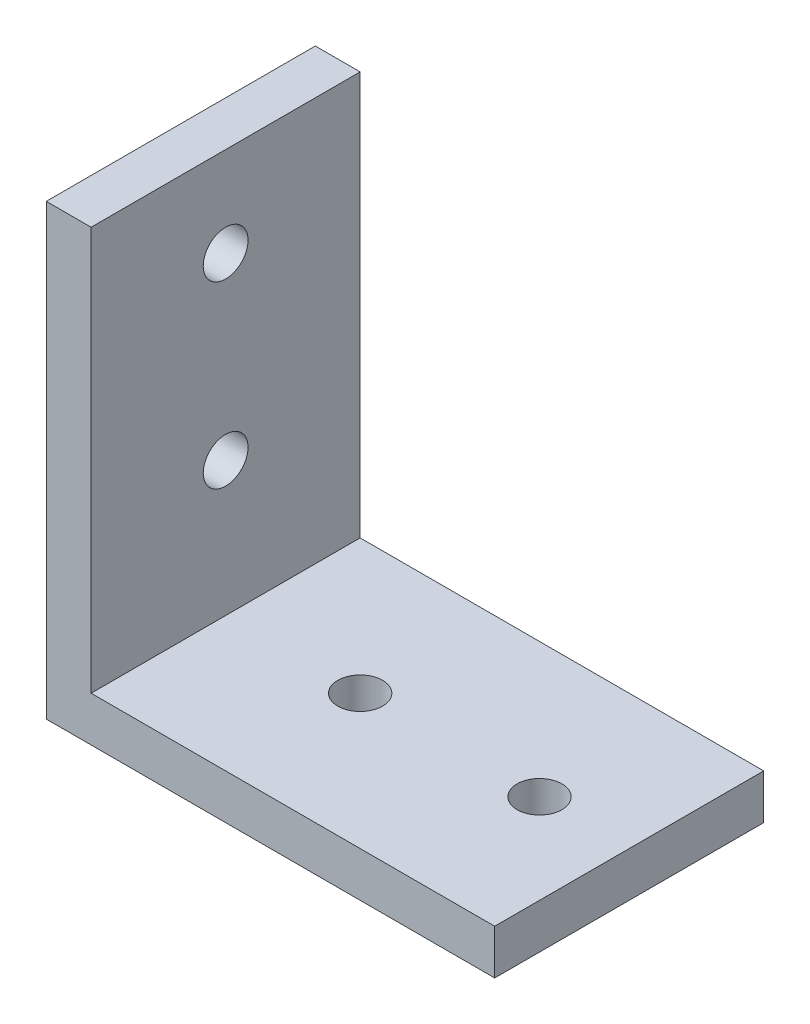
SolidWorks part; units mm, degrees
material "Plain Carbon Steel"
ref_plane "Front Plane" through (0, 0, 0) normal (0, 0, 1) x (1, 0, 0)
ref_plane "Top Plane" through (0, 0, 0) normal (0, 1, 0) x (1, 0, 0)
ref_plane "Right Plane" through (0, 0, 0) normal (1, 0, 0) x (0, 0, -1)
sketch "Sketch1" plane through (0, 0, 0) normal (0, 0, 1) x (1, 0, 0)
  line L0 (0, 0) -> (0, 100)
  line L1 (0, 100) -> (10, 100)
  line L2 (10, 100) -> (10, 10)
  line L3 (10, 10) -> (100, 10)
  line L4 (100, 10) -> (100, 0)
  line L5 (100, 0) -> (0, 0)
  dimension "D1" = 10
  dimension "D2" = 100
  dimension "D3" = 100
extrude "Boss-Extrude1" add sketch "Sketch1" along normal mid plane 60
sketch "Sketch2" plane through (10, 0, 0) normal (1, 0, 0) x (0, 0, -1)
  line L0 (-30, 0) -> (30, 0) construction
  line L1 (0, 55) -> (0, -55) construction
  circle A0 centre (0, 40) radius 5
  circle A1 centre (0, 80) radius 5
  dimension "D1" = 10
  dimension "D2" = 40
  dimension "D3" = 80
extrude "Cut-Extrude1" cut sketch "Sketch2" against normal through all
sketch "Sketch3" plane through (0, 10, 0) normal (0, 1, 0) x (0, 0, -1)
  line L1 (0, 55) -> (0, -55) construction
  line L2 (-30, 0) -> (30, 0) construction
  circle A0 centre (0, -80) radius 5
  circle A1 centre (0, -40) radius 5
  dimension "D1" = 10
  dimension "D2" = 40
  dimension "D3" = 80
extrude "Cut-Extrude2" cut sketch "Sketch3" against normal through all
